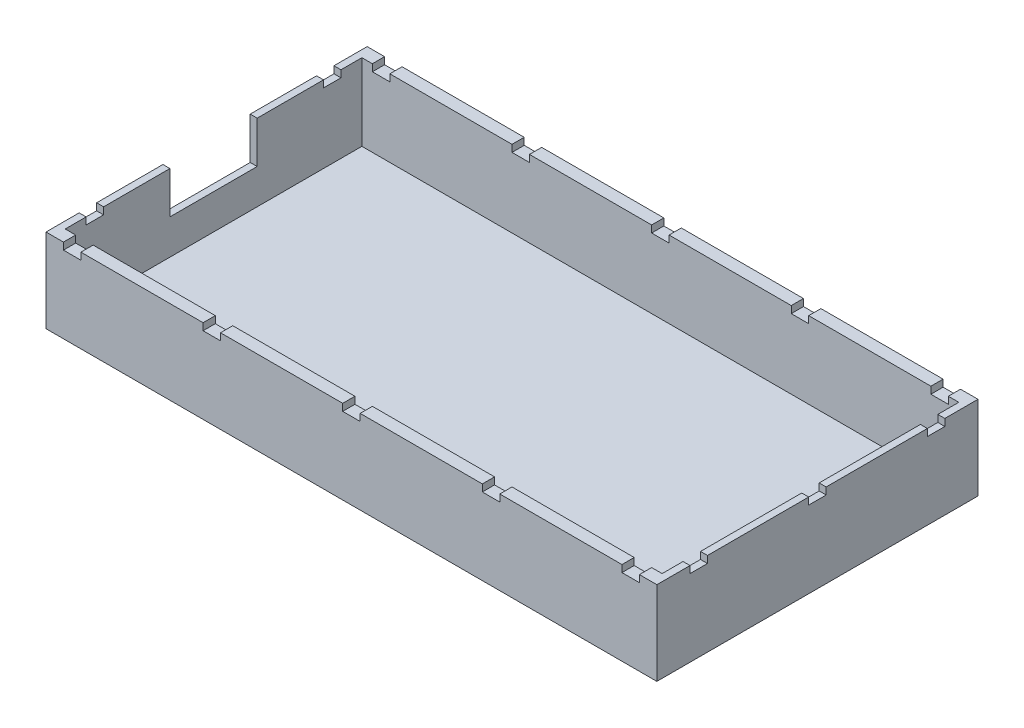
SolidWorks part; units mm, degrees
ref_plane "Front Plane" through (0, 0, 0) normal (0, 0, 1) x (1, 0, 0)
ref_plane "Top Plane" through (0, 0, 0) normal (0, 1, 0) x (1, 0, 0)
ref_plane "Right Plane" through (0, 0, 0) normal (1, 0, 0) x (0, 0, -1)
sketch "Sketch1" plane through (0, 0, 0) normal (0, 1, 0) x (1, 0, 0)
  line L1 (87.5, 46) -> (-87.5, 46)
  line L2 (87.5, 46) -> (87.5, -46)
  line L3 (87.5, -46) -> (-87.5, -46)
  line L4 (-87.5, 46) -> (-87.5, -46)
  line L5 (87.5, 46) -> (-87.5, -46) construction
  line L6 (87.5, -46) -> (-87.5, 46) construction
  point P0 (0, 0)
  dimension "D1" = 175
  dimension "D2" = 92
extrude "Boss-Extrude1" add sketch "Sketch1" along normal blind 24
sketch "Sketch2" plane through (0, 24, 0) normal (0, 1, 0) x (1, 0, 0)
  line L1 (85.5, -42.5) -> (-85.5, -42.5)
  line L2 (85.5, -42.5) -> (85.5, 42.5)
  line L3 (85.5, 42.5) -> (-85.5, 42.5)
  line L4 (-85.5, -42.5) -> (-85.5, 42.5)
  line L5 (85.5, -42.5) -> (-85.5, 42.5) construction
  line L6 (85.5, 42.5) -> (-85.5, -42.5) construction
  point P0 (0, 0)
  dimension "D1" = 85
  dimension "D2" = 171
extrude "Cut-Extrude1" cut sketch "Sketch2" against normal blind 22
sketch "Sketch3" plane through (-87.5, 0, 0) normal (-1, 0, 0) x (0, 0, 1)
  line L0 (0, 0) -> (0, 46.3856) construction
  line L1 (-46, 0) -> (46, 0) construction
  line L2 (-46, 24) -> (46, 24) construction
  line L3 (12.5, 12) -> (-12.5, 12)
  line L4 (12.5, 12) -> (12.5, 24)
  line L5 (12.5, 24) -> (-12.5, 24)
  line L6 (-12.5, 12) -> (-12.5, 24)
  line L7 (12.5, 12) -> (-12.5, 24) construction
  line L8 (12.5, 24) -> (-12.5, 12) construction
  point P4 (0, 18)
  dimension "D1" = 25
  dimension "D2" = 12
extrude "Cut-Extrude2" cut sketch "Sketch3" against normal blind 2
sketch "Sketch4" plane through (0, 24, 0) normal (0, 1, 0) x (1, 0, 0)
  line L0 (87.5, 46) -> (-87.5, 46) construction
  line L1 (-82.5, 46) -> (-77.5, 46)
  line L2 (-82.5, 46) -> (-82.5, 42.5)
  line L3 (-82.5, 42.5) -> (-77.5, 42.5)
  line L4 (-77.5, 46) -> (-77.5, 42.5)
  line L5 (-82.5, 46) -> (-77.5, 42.5) construction
  line L6 (-82.5, 42.5) -> (-77.5, 46) construction
  line L7 (85.5, 42.5) -> (-85.5, 42.5) construction
  line L8 (-87.5, 44.25) -> (-80, 44.25) construction
  line L9 (-87.5, 46) -> (-87.5, 12.5) construction
  line L10 (87.5, 44.25) -> (80, 44.25) construction
  line L11 (87.5, -46) -> (87.5, 46) construction
  line L12 (-42.5, 46) -> (-42.5, 42.5)
  line L13 (-42.5, 46) -> (-37.5, 46)
  line L14 (-37.5, 46) -> (-37.5, 42.5)
  line L15 (-42.5, 42.5) -> (-37.5, 42.5)
  line L16 (-2.5, 46) -> (-2.5, 42.5)
  line L17 (-2.5, 46) -> (2.5, 46)
  line L18 (2.5, 46) -> (2.5, 42.5)
  line L19 (-2.5, 42.5) -> (2.5, 42.5)
  line L20 (37.5, 46) -> (37.5, 42.5)
  line L21 (37.5, 46) -> (42.5, 46)
  line L22 (42.5, 46) -> (42.5, 42.5)
  line L23 (37.5, 42.5) -> (42.5, 42.5)
  line L24 (77.5, 46) -> (77.5, 42.5)
  line L25 (77.5, 46) -> (82.5, 46)
  line L26 (82.5, 46) -> (82.5, 42.5)
  line L27 (77.5, 42.5) -> (82.5, 42.5)
  point P4 (-80, 44.25)
  dimension "D1" = 5
  dimension "D2" = 7.5
  dimension "D3" = 5
extrude "Cut-Extrude4" cut sketch "Sketch4" against normal blind 2
sketch "Sketch5" plane through (0, 24, 0) normal (0, 1, 0) x (1, 0, 0)
  line L0 (-87.5, -44.25) -> (-80, -44.25) construction
  line L1 (-87.5, -12.5) -> (-87.5, -46) construction
  line L2 (87.5, -44.25) -> (80, -44.25) construction
  line L3 (87.5, -46) -> (87.5, 46) construction
  line L4 (-87.5, -46) -> (87.5, -46) construction
  line L5 (-82.5, -42.5) -> (-77.5, -42.5)
  line L6 (-82.5, -42.5) -> (-82.5, -46)
  line L7 (-82.5, -46) -> (-77.5, -46)
  line L8 (-77.5, -42.5) -> (-77.5, -46)
  line L9 (-82.5, -42.5) -> (-77.5, -46) construction
  line L10 (-82.5, -46) -> (-77.5, -42.5) construction
  line L11 (-42.5, -42.5) -> (-42.5, -46)
  line L12 (-42.5, -42.5) -> (-37.5, -42.5)
  line L13 (-37.5, -42.5) -> (-37.5, -46)
  line L14 (-42.5, -46) -> (-37.5, -46)
  line L15 (-2.5, -42.5) -> (-2.5, -46)
  line L16 (-2.5, -42.5) -> (2.5, -42.5)
  line L17 (2.5, -42.5) -> (2.5, -46)
  line L18 (-2.5, -46) -> (2.5, -46)
  line L19 (37.5, -42.5) -> (37.5, -46)
  line L20 (37.5, -42.5) -> (42.5, -42.5)
  line L21 (42.5, -42.5) -> (42.5, -46)
  line L22 (37.5, -46) -> (42.5, -46)
  line L23 (77.5, -42.5) -> (77.5, -46)
  line L24 (77.5, -42.5) -> (82.5, -42.5)
  line L25 (82.5, -42.5) -> (82.5, -46)
  line L26 (77.5, -46) -> (82.5, -46)
  dimension "D1" = 7.5
  dimension "D2" = 7.5
  dimension "D3" = 5
  dimension "D4" = 5
  dimension "D5" = 3.5
extrude "Cut-Extrude7" cut sketch "Sketch5" against normal blind 2
sketch "Sketch7" plane through (0, 24, 0) normal (0, 1, 0) x (1, 0, 0)
  line L0 (86.5, 46) -> (86.5, 34) construction
  line L1 (85.5, 2.5) -> (87.5, 2.5)
  line L2 (85.5, -2.5) -> (87.5, -2.5)
  line L3 (87.5, 46) -> (82.5, 46) construction
  line L4 (86.5, -46) -> (86.5, -34) construction
  line L5 (82.5, -46) -> (87.5, -46) construction
  line L6 (87.5, 2.5) -> (87.5, -2.5)
  line L11 (87.5, -46) -> (87.5, 46) construction
  line L12 (85.5, -31.5) -> (87.5, -31.5)
  line L13 (85.5, -31.5) -> (85.5, -36.5)
  line L14 (85.5, -36.5) -> (87.5, -36.5)
  line L15 (87.5, -31.5) -> (87.5, -36.5)
  line L16 (85.5, -31.5) -> (87.5, -36.5) construction
  line L17 (85.5, -36.5) -> (87.5, -31.5) construction
  line L18 (85.5, 2.5) -> (85.5, -2.5)
  line L19 (85.5, 36.5) -> (87.5, 36.5)
  line L20 (85.5, 31.5) -> (87.5, 31.5)
  line L21 (87.5, 36.5) -> (87.5, 31.5)
  line L22 (85.5, 36.5) -> (85.5, 31.5)
  dimension "D1" = 12
  dimension "D2" = 12
  dimension "D3" = 5
  dimension "D4" = 3
extrude "Cut-Extrude8" cut sketch "Sketch7" against normal blind 2
sketch "Sketch10" plane through (0, 24, 0) normal (0, 1, 0) x (1, 0, 0)
  line L0 (-87.5, 46) -> (-87.5, 12.5) construction
  line L1 (-87.5, 36.5) -> (-85.5, 36.5)
  line L2 (-87.5, 36.5) -> (-87.5, 31.5)
  line L3 (-87.5, 31.5) -> (-85.5, 31.5)
  line L4 (-85.5, 36.5) -> (-85.5, 31.5)
  line L5 (-87.5, 36.5) -> (-85.5, 31.5) construction
  line L6 (-87.5, 31.5) -> (-85.5, 36.5) construction
  line L7 (-85.5, 42.5) -> (-85.5, 12.5) construction
  line L8 (-82.5, 46) -> (-87.5, 46) construction
  point P4 (-86.5, 34)
  dimension "D1" = 5
  dimension "D2" = 12
extrude "Cut-Extrude9" cut sketch "Sketch10" against normal blind 2
sketch "Sketch11" plane through (0, 24, 0) normal (0, 1, 0) x (1, 0, 0)
  line L0 (-85.5, -12.5) -> (-85.5, -42.5) construction
  line L1 (-85.5, -31.5) -> (-87.5, -31.5)
  line L2 (-85.5, -31.5) -> (-85.5, -36.5)
  line L3 (-85.5, -36.5) -> (-87.5, -36.5)
  line L4 (-87.5, -31.5) -> (-87.5, -36.5)
  line L5 (-85.5, -31.5) -> (-87.5, -36.5) construction
  line L6 (-85.5, -36.5) -> (-87.5, -31.5) construction
  line L7 (-87.5, -12.5) -> (-87.5, -46) construction
  line L8 (-87.5, -46) -> (-82.5, -46) construction
  point P4 (-86.5, -34)
  dimension "D1" = 5
  dimension "D2" = 12
extrude "Cut-Extrude10" cut sketch "Sketch11" against normal blind 2
